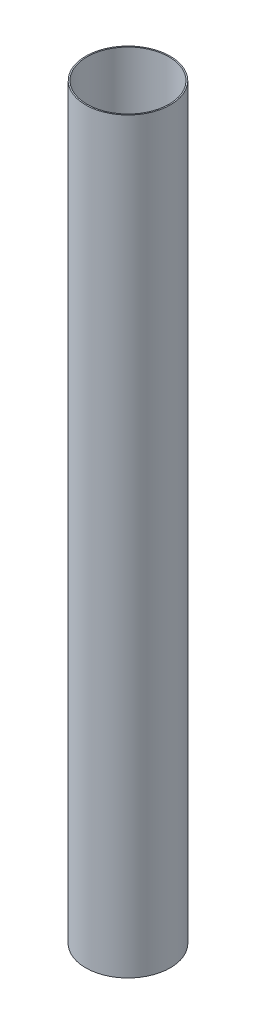
SolidWorks part; units mm, degrees
ref_plane "Front Plane" through (0, 0, 0) normal (0, 0, 1) x (1, 0, 0)
ref_plane "Top Plane" through (0, 0, 0) normal (0, 1, 0) x (1, 0, 0)
ref_plane "Right Plane" through (0, 0, 0) normal (1, 0, 0) x (0, 0, -1)
sketch "Sketch1" plane through (0, 0, 0) normal (0, 1, 0) x (1, 0, 0)
  circle A0 centre (0, 0) radius 65.405
  circle A1 centre (0, 0) radius 63.5
  dimension "D1" = 130.81
  dimension "D2" = 127
extrude "Boss-Extrude1" add sketch "Sketch1" along normal mid plane 1155.7
equation "\"iDiameter\"= 5in"
equation "\"oDiameter\"= 5.15in"
equation "\"length\"= 35.5in"
